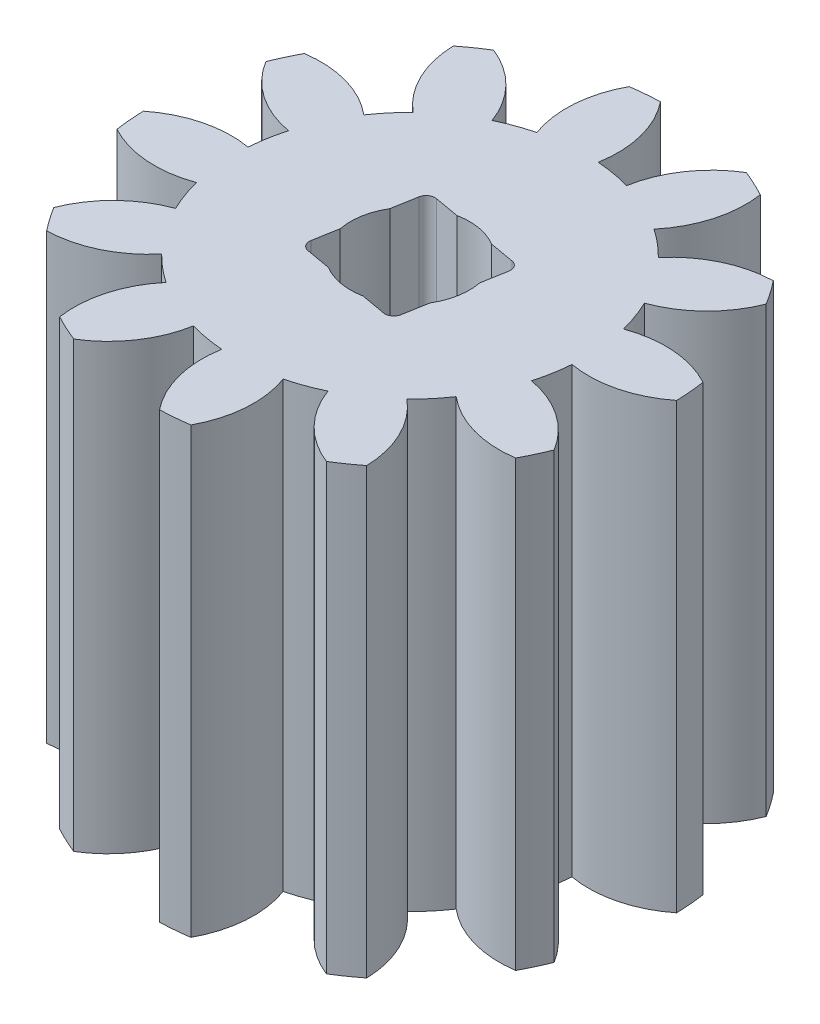
SolidWorks part; units mm, degrees
material "Custom Plastic"
ref_plane "Front Plane" through (0, 0, 0) normal (0, 0, 1) x (1, 0, 0)
ref_plane "Top Plane" through (0, 0, 0) normal (0, 1, 0) x (1, 0, 0)
ref_plane "Right Plane" through (0, 0, 0) normal (1, 0, 0) x (0, 0, -1)
ref_plane "Plane1" through (0, -6.35, 0) normal (0, -1, 0) x (1, 0, 0)
sketch "Sketch1" plane through (0, -6.35, 0) normal (0, -1, 0) x (1, 0, 0)
  line L0 (1.3318, 1.5889) -> (1.7949, -1.0376)
  line L1 (1.5889, -1.3318) -> (-1.0376, -1.7949)
  line L2 (-1.3318, -1.5889) -> (-1.7949, 1.0376)
  line L3 (-1.5889, 1.3318) -> (1.0376, 1.7949)
  arc A0 (3.9007, 6.2931) -> (2.1801, 4.528) centre (4.999, 3.5014) ccw
  arc A1 (2.1801, 4.528) -> (1.2404, 4.87) centre (0, 0) ccw
  arc A2 (1.2404, 4.87) -> (1.057, 7.3282) centre (-1.5788, 5.8955) ccw
  arc A3 (1.057, 7.3282) -> (0.2316, 7.4004) centre (0, 0) ccw
  arc A4 (0.2316, 7.4004) -> (-0.3759, 5.0114) centre (2.5786, 5.5318) ccw
  arc A5 (-0.3759, 5.0114) -> (-1.3607, 4.8378) centre (0, 0) ccw
  arc A6 (-1.3607, 4.8378) -> (-2.7487, 6.8749) centre (-4.3151, 4.3163) ccw
  arc A7 (-2.7487, 6.8749) -> (-3.4996, 6.5247) centre (0, 0) ccw
  arc A8 (-3.4996, 6.5247) -> (-2.8313, 4.152) centre (-0.5328, 6.08) ccw
  arc A9 (-2.8313, 4.152) -> (-3.5973, 3.5093) centre (0, 0) ccw
  arc A10 (-3.5973, 3.5093) -> (-5.8179, 4.5795) centre (-5.8951, 1.5805) ccw
  arc A11 (-5.8179, 4.5795) -> (-6.2931, 3.9007) centre (0, 0) ccw
  arc A12 (-6.2931, 3.9007) -> (-4.528, 2.1801) centre (-3.5014, 4.999) ccw
  arc A13 (-4.528, 2.1801) -> (-4.87, 1.2404) centre (0, 0) ccw
  arc A14 (-4.87, 1.2404) -> (-7.3282, 1.057) centre (-5.8955, -1.5788) ccw
  arc A15 (-7.3282, 1.057) -> (-7.4004, 0.2316) centre (0, 0) ccw
  arc A16 (-7.4004, 0.2316) -> (-5.0114, -0.3759) centre (-5.5318, 2.5786) ccw
  arc A17 (-5.0114, -0.3759) -> (-4.8378, -1.3607) centre (0, 0) ccw
  arc A18 (-4.8378, -1.3607) -> (-6.8749, -2.7487) centre (-4.3163, -4.3151) ccw
  arc A19 (-6.8749, -2.7487) -> (-6.5247, -3.4996) centre (0, 0) ccw
  arc A20 (-6.5247, -3.4996) -> (-4.152, -2.8313) centre (-6.08, -0.5328) ccw
  arc A21 (-4.152, -2.8313) -> (-3.5093, -3.5973) centre (0, 0) ccw
  arc A22 (-3.5093, -3.5973) -> (-4.5795, -5.8179) centre (-1.5805, -5.8951) ccw
  arc A23 (-4.5795, -5.8179) -> (-3.9007, -6.2931) centre (0, 0) ccw
  arc A24 (-3.9007, -6.2931) -> (-2.1801, -4.528) centre (-4.999, -3.5014) ccw
  arc A25 (-2.1801, -4.528) -> (-1.2404, -4.87) centre (0, 0) ccw
  arc A26 (-1.2404, -4.87) -> (-1.057, -7.3282) centre (1.5788, -5.8955) ccw
  arc A27 (-1.057, -7.3282) -> (-0.2316, -7.4004) centre (0, 0) ccw
  arc A28 (-0.2316, -7.4004) -> (0.3759, -5.0114) centre (-2.5786, -5.5318) ccw
  arc A29 (0.3759, -5.0114) -> (1.3607, -4.8378) centre (0, 0) ccw
  arc A30 (1.3607, -4.8378) -> (2.7487, -6.8749) centre (4.3151, -4.3163) ccw
  arc A31 (2.7487, -6.8749) -> (3.4996, -6.5247) centre (0, 0) ccw
  arc A32 (3.4996, -6.5247) -> (2.8313, -4.152) centre (0.5328, -6.08) ccw
  arc A33 (2.8313, -4.152) -> (3.5973, -3.5093) centre (0, 0) ccw
  arc A34 (3.5973, -3.5093) -> (5.8179, -4.5795) centre (5.8951, -1.5805) ccw
  arc A35 (5.8179, -4.5795) -> (6.2931, -3.9007) centre (0, 0) ccw
  arc A36 (6.2931, -3.9007) -> (4.528, -2.1801) centre (3.5014, -4.999) ccw
  arc A37 (4.528, -2.1801) -> (4.87, -1.2404) centre (0, 0) ccw
  arc A38 (4.87, -1.2404) -> (7.3282, -1.057) centre (5.8955, 1.5788) ccw
  arc A39 (7.3282, -1.057) -> (7.4004, -0.2316) centre (0, 0) ccw
  arc A40 (7.4004, -0.2316) -> (5.0114, 0.3759) centre (5.5318, -2.5786) ccw
  arc A41 (5.0114, 0.3759) -> (4.8378, 1.3607) centre (0, 0) ccw
  arc A42 (4.8378, 1.3607) -> (6.8749, 2.7487) centre (4.3163, 4.3151) ccw
  arc A43 (6.8749, 2.7487) -> (6.5247, 3.4996) centre (0, 0) ccw
  arc A44 (6.5247, 3.4996) -> (4.152, 2.8313) centre (6.08, 0.5328) ccw
  arc A45 (4.152, 2.8313) -> (3.5093, 3.5973) centre (0, 0) ccw
  arc A46 (3.5093, 3.5973) -> (4.5795, 5.8179) centre (1.5805, 5.8951) ccw
  arc A47 (4.5795, 5.8179) -> (3.9007, 6.2931) centre (0, 0) ccw
  arc A48 (1.0376, 1.7949) -> (1.3318, 1.5889) centre (1.0817, 1.5448) cw
  arc A49 (1.7949, -1.0376) -> (1.5889, -1.3318) centre (1.5448, -1.0817) cw
  arc A50 (-1.0376, -1.7949) -> (-1.3318, -1.5889) centre (-1.0817, -1.5448) cw
  arc A51 (-1.7949, 1.0376) -> (-1.5889, 1.3318) centre (-1.5448, 1.0817) cw
extrude "Boss-Extrude1" add sketch "Sketch1" against normal blind 12.7
sketch "Sketch2" plane through (0, 6.35, 0) normal (0, 1, 0) x (1, 0, 0)
  circle A0 centre (0, 0) radius 1.7018
extrude "Cut-Extrude1" cut sketch "Sketch2" against normal blind 56.896
